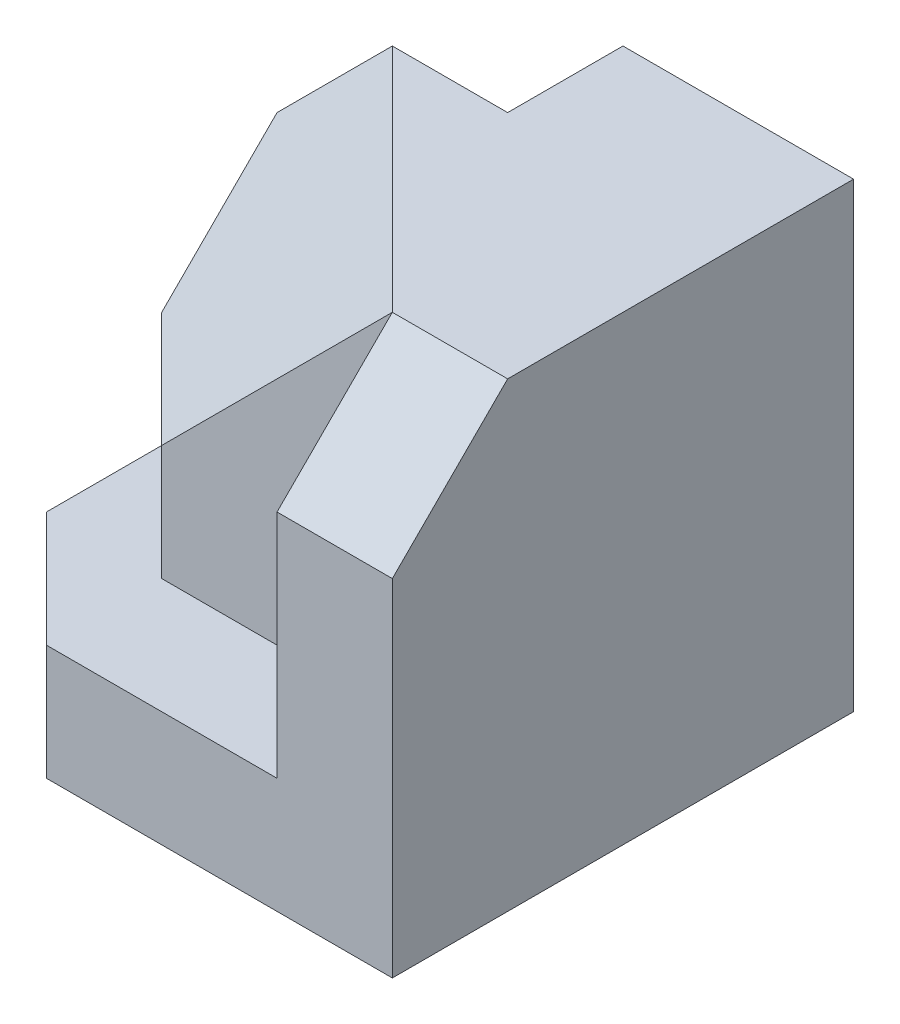
SolidWorks part; units mm, degrees
ref_plane "Front Plane" through (0, 0, 0) normal (0, 0, 1) x (1, 0, 0)
ref_plane "Top Plane" through (0, 0, 0) normal (0, 1, 0) x (1, 0, 0)
ref_plane "Right Plane" through (0, 0, 0) normal (1, 0, 0) x (0, 0, -1)
sketch "Sketch2" plane through (0, 0, 0) normal (0, 1, 0) x (1, 0, 0)
  line L0 (0, 0) -> (10, 0)
  line L1 (10, 0) -> (10, -15)
  line L2 (10, -15) -> (5, -15)
  line L3 (5, -15) -> (-5, -5)
  line L4 (-5, -5) -> (0, -5)
  line L5 (0, -5) -> (0, 0)
  dimension "D1" = 5
  dimension "D2" = 5
  dimension "D3" = 10
  dimension "D4" = 15
  dimension "D5" = 5
extrude "Boss-Extrude2" add sketch "Sketch2" along normal blind 20
sketch "Sketch3" plane through (0, 0, 15) normal (0, 0, 1) x (1, 0, 0)
  line L1 (5, 0) -> (10, 0)
  line L2 (5, 0) -> (5, 20)
  line L3 (5, 20) -> (10, 20)
  line L4 (10, 0) -> (10, 20)
extrude "Boss-Extrude4" add sketch "Sketch3" along normal blind 5
sketch "Sketch4" plane through (5, 0, 0) normal (-1, 0, 0) x (0, 0, 1)
  line L0 (15, 20) -> (20, 15)
  line L1 (20, 20) -> (20, 0) construction
  line L2 (20, 15) -> (20, 20)
  line L3 (20, 20) -> (15, 20)
  dimension "D1" = 5
extrude "Cut-Extrude1" cut sketch "Sketch4" against normal blind 5
sketch "Sketch5" plane through (0, 0, 0) normal (-1, 0, 0) x (0, 0, 1)
  line L1 (0, 0) -> (5, 0)
  line L2 (0, 0) -> (0, 20)
  line L3 (0, 20) -> (5, 20)
  line L4 (5, 0) -> (5, 20)
extrude "Boss-Extrude5" add sketch "Sketch5" along normal blind 5
sketch "Sketch6" plane through (0, 0, 0) normal (0, 0, -1) x (-1, 0, 0)
  line L0 (0, 20) -> (5, 20)
  line L1 (-10, 20) -> (5, 20) construction
  line L2 (5, 20) -> (5, 15)
  line L3 (5, 20) -> (5, 0) construction
  line L4 (5, 15) -> (0, 20)
  dimension "D1" = 5
  dimension "D2" = 5
extrude "Cut-Extrude2" cut sketch "Sketch6" against normal blind 5
sketch "Sketch7" plane through (-5, 0, 0) normal (-1, 0, 0) x (0, 0, 1)
  line L1 (0, 0) -> (5, 0)
  line L2 (0, 0) -> (0, 15)
  line L3 (0, 15) -> (5, 15)
  line L4 (5, 0) -> (5, 15)
extrude "Boss-Extrude6" add sketch "Sketch7" along normal blind 5
ref_plane "Plane1" through (0, 0, 0) normal (0, -1, 0) x (-1, 0, 0)
sketch "Sketch8" plane through (0, 0, 0) normal (0, -1, 0) x (-1, 0, 0)
  line L0 (10, -5) -> (5, -5)
  line L1 (5, -5) -> (-5, -15)
  line L2 (-5, -15) -> (5, -15)
  line L3 (5, -15) -> (10, -10)
  line L4 (10, -10) -> (10, -5)
  dimension "D1" = 5
  dimension "D2" = 10
  dimension "D3" = 5
extrude "Boss-Extrude7" add sketch "Sketch8" against normal blind 20
sketch3d "3DSketch1"
  line L0 (-10, 20, 5) -> (0, 20, 5) construction
  line L1 (-10, 20, 10) -> (-10, 0, 10) construction
  line L2 (-5, 20, 15) -> (-5, 0, 15) construction
  line L3 (-5, 20, 15) -> (-10, 20, 10) construction
  line L4 (-5, 10, 15) -> (5, 20, 15)
  line L5 (5, 20, 15) -> (-5, 20, 5)
  line L6 (-5, 20, 5) -> (-10, 15, 5)
  line L7 (-10, 15, 5) -> (-10, 10, 10)
  line L8 (-10, 10, 10) -> (-5, 10, 15)
  point P0 (-5, 20, 5)
  point P1 (5, 20, 15)
  point P5 (-10, 15, 5)
  point P7 (-10, 10, 10)
  point P9 (-5, 10, 15)
  dimension "D1" = 5
  dimension "D2" = 10
  dimension "D3" = 10
extrude "Cut-Extrude3" cut sketch "3DSketch1" along direction (0, -1, 0) on the side of the normal blind 20
sketch "Sketch9" plane through (0, 0, 0) normal (0, -1, 0) x (-1, 0, 0)
  line L0 (10, -10) -> (5, -15)
  line L1 (5, -15) -> (-5, -15)
  line L2 (-5, -15) -> (-5, -20)
  line L3 (-5, -20) -> (5, -20)
  line L4 (5, -20) -> (10, -15)
  line L5 (10, -15) -> (10, -10)
  dimension "D1" = 5
  dimension "D2" = 10
extrude "Boss-Extrude8" add sketch "Sketch9" against normal blind 5 contours L4 L5 L0 L1 L2 L3
sketch "Sketch10" plane through (0, 5, 0) normal (0, 1, 0) x (1, 0, 0)
  line L0 (0, -15) -> (5, -20)
  line L1 (-5, -15) -> (5, -15) construction
  line L2 (5, -20) -> (5, -15)
  line L3 (5, -15) -> (0, -15)
  dimension "D1" = 5
extrude "Boss-Extrude9" add sketch "Sketch10" along normal blind 5
